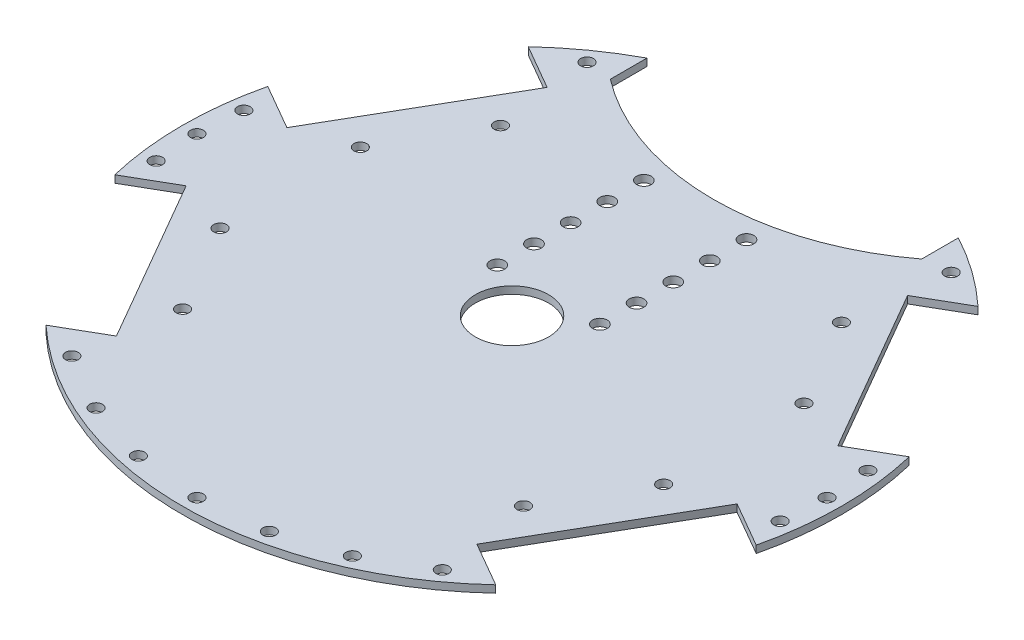
SolidWorks part; units mm, degrees
ref_plane "Front Plane" through (0, 0, 0) normal (0, 0, 1) x (1, 0, 0)
ref_plane "Top Plane" through (0, 0, 0) normal (0, 1, 0) x (1, 0, 0)
ref_plane "Right Plane" through (0, 0, 0) normal (1, 0, 0) x (0, 0, -1)
sketch "Sketch1" plane through (0, 0, 0) normal (0, 1, 0) x (1, 0, 0)
  circle A0 centre (0, 0) radius 90
extrude "Boss-Extrude1" add sketch "Sketch1" along normal blind 2
sketch "Sketch3" plane through (0, 2, 0) normal (0, 1, 0) x (1, 0, 0)
  line L0 (-106.3742, 31.7534) -> (-80.3742, 76.7867)
  line L1 (-106.3742, 31.7534) -> (-75.1973, 13.7534)
  line L2 (0, 0) -> (0, -20) construction
  line L3 (0, -20) -> (-77.7858, 45.27) construction
  line L4 (-80.3742, 76.7867) -> (-49.1973, 58.7867)
  line L5 (-75.1973, 13.7534) -> (-49.1973, 58.7867)
  line L6 (-106.3742, 31.7534) -> (-49.1973, 58.7867) construction
  line L7 (-80.3742, 76.7867) -> (-75.1973, 13.7534) construction
  circle A0 centre (0, 0) radius 90 construction
  dimension "D1" = 50
  dimension "D2" = 20
  dimension "D3" = 18
  dimension "D4" = 52
  dimension "D5" = 80
extrude "Cut-Extrude1" cut sketch "Sketch3" against normal through all
sketch "Sketch5" plane through (0, 2, 0) normal (0, 1, 0) x (1, 0, 0)
  line L0 (-62.1973, 36.27) -> (-53.5371, 31.27) construction
  line L1 (-75.1973, 13.7534) -> (-49.1973, 58.7867) construction
  line L2 (-53.5371, 31.27) -> (-60.5371, 19.1457) construction
  line L3 (-53.5371, 31.27) -> (-46.5371, 43.3944) construction
  circle A0 centre (-60.5371, 19.1457) radius 1.75
  circle A1 centre (-46.5371, 43.3944) radius 1.75
  dimension "D1" = 3.5
  dimension "D2" = 3.5
  dimension "D3" = 10
  dimension "D4" = 14
  dimension "D5" = 14
extrude "Cut-Extrude3" cut sketch "Sketch5" against normal through all
mirror "Mirror1" about plane through (0, 0, 0) normal (0, 0, 1) of "Cut-Extrude3", "Cut-Extrude1"
mirror "Mirror2" about plane through (0, 0, 0) normal (1, 0, 0) of "Mirror1", "Cut-Extrude1", "Cut-Extrude3"
sketch "Sketch4" plane through (0, 2, 0) normal (0, 1, 0) x (1, 0, 0)
  line L0 (0, 90) -> (0, 55) construction
  line L1 (-42.5, 79.3332) -> (-42.5, 69.3332)
  line L2 (42.5, 79.3332) -> (42.5, 69.3332)
  line L3 (-42.5, 79.3332) -> (-42.5, 105.8098)
  line L4 (-42.5, 105.8098) -> (42.5, 105.8098)
  line L5 (42.5, 105.8098) -> (42.5, 79.3332)
  arc A0 (61.3809, 65.8209) -> (-61.3809, 65.8209) centre (0, 0) ccw construction
  arc A1 (-42.5, 69.3332) -> (42.5, 69.3332) centre (0, 125.1761) ccw
  dimension "D1" = 35
  dimension "D2" = 42.5
  dimension "D3" = 42.5
  dimension "D4" = 10
  dimension "D5" = 10
extrude "Cut-Extrude2" cut sketch "Sketch4" against normal through all
sketch "Sketch6" plane through (0, 2, 0) normal (0, 1, 0) x (1, 0, 0)
  circle A0 centre (0, 0) radius 10
extrude "Cut-Extrude4" cut sketch "Sketch6" against normal through all
sketch "Sketch7" plane through (0, 0, 0) normal (0, -1, 0) x (1, 0, 0)
  circle A0 centre (0, 86) radius 1.75
  arc A1 (61.3809, 65.8209) -> (-61.3809, 65.8209) centre (0, 0) ccw construction
  dimension "D2" = 3.5
  dimension "D1" = 86
extrude "Cut-Extrude5" cut sketch "Sketch7" against normal through all
pattern_circular "CirPattern1" count 4 every 12 about axis through (0, 0, 0) along (0, 1, 0) of "Cut-Extrude5"
sketch "Sketch8" plane through (0, 2, 0) normal (0, 1, 0) x (1, 0, 0)
  circle A0 centre (-86, 0) radius 1.75
  arc A1 (-87.544, 20.8817) -> (-87.544, -20.8817) centre (0, 0) ccw construction
  dimension "D2" = 3.5
  dimension "D1" = 86
extrude "Cut-Extrude6" cut sketch "Sketch8" against normal through all
sketch "Sketch9" plane through (0, 2, 0) normal (0, 1, 0) x (1, 0, 0)
  circle A0 centre (-49.7064, 70.1803) radius 1.75
  arc A1 (-42.5, 79.3332) -> (-61.3809, 65.8209) centre (0, 0) ccw construction
  dimension "D2" = 3.5
  dimension "D1" = 86
extrude "Cut-Extrude7" cut sketch "Sketch9" against normal through all
pattern_circular "CirPattern2" count 2 every 8 about axis through (0, 2, 0) along (0, 1, 0) of "Cut-Extrude6"
mirror "Mirror3" about plane through (0, 0, 0) normal (1, 0, 0) of "Cut-Extrude7", "Cut-Extrude6", "CirPattern2"
sketch "Sketch10" plane through (0, 2, 0) normal (0, 1, 0) x (1, 0, 0)
  line L0 (0, 0) -> (0, 50) construction
  line L1 (0, 50) -> (14, 50) construction
  circle A0 centre (14, 50) radius 2
  dimension "D2" = 4
  dimension "D1" = 14
  dimension "D3" = 50
extrude "Cut-Extrude8" cut sketch "Sketch10" against normal through all
mirror "Mirror4" about plane through (0, 0, 0) normal (1, 0, 0) of "Cut-Extrude8"
pattern_linear "LPattern1" count 5 spacing 10 along (0, 0, 1) of "Cut-Extrude8", "Mirror4"
